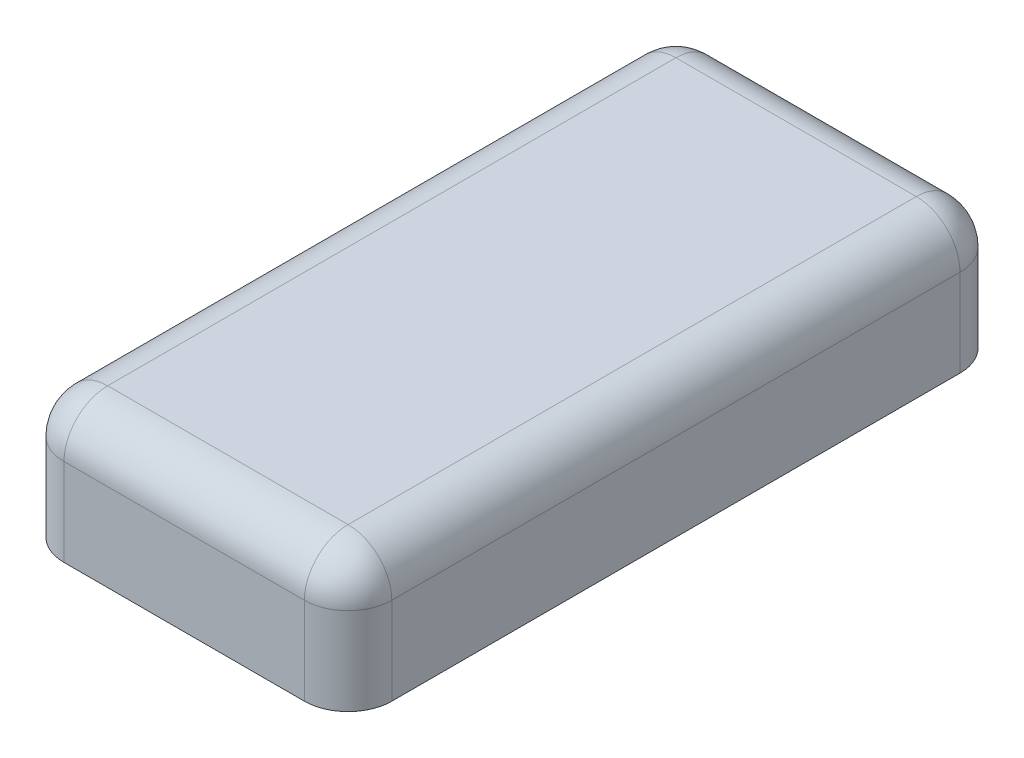
SolidWorks part; units mm, degrees
ref_plane "Front Plane" through (0, 0, 0) normal (0, 0, 1) x (1, 0, 0)
ref_plane "Top Plane" through (0, 0, 0) normal (0, 1, 0) x (1, 0, 0)
ref_plane "Right Plane" through (0, 0, 0) normal (1, 0, 0) x (0, 0, -1)
sketch "BaseS" plane through (0, 0, 0) normal (0, 1, 0) x (1, 0, 0)
  line L1 (-0.75, 1.5) -> (0.75, 1.5)
  line L2 (-0.75, 1.5) -> (-0.75, -1.5)
  line L3 (-0.75, -1.5) -> (0.75, -1.5)
  line L4 (0.75, 1.5) -> (0.75, -1.5)
  line L5 (-0.75, 1.5) -> (0.75, -1.5) construction
  line L6 (-0.75, -1.5) -> (0.75, 1.5) construction
  point P0 (0, 0)
  dimension "Width" = 1.5
  dimension "Length" = 3
extrude "Base" add sketch "BaseS" along normal blind 0.6
fillet "SideF" radius 0.2 4 edges at (0.75, 0.3, 1.5) (0.75, 0.3, -1.5) (-0.75, 0.3, 1.5) (-0.75, 0.3, -1.5)
fillet "TopF" radius 0.2 8 edges at (-0.6914, 0.6, 1.4414) (-0.75, 0.6, 0) (-0.6914, 0.6, -1.4414) (0, 0.6, -1.5) (0.6914, 0.6, -1.4414) (0.75, 0.6, 0) (0.6914, 0.6, 1.4414) (0, 0.6, 1.5)
